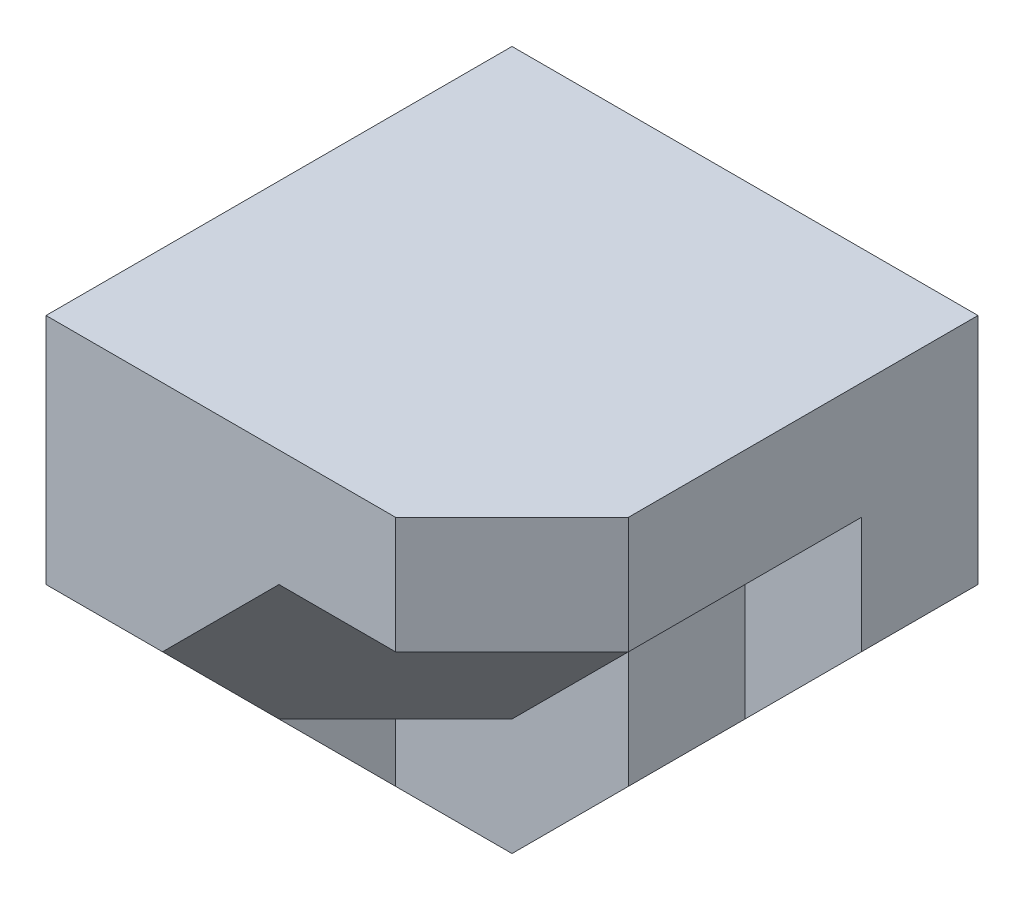
SolidWorks part; units mm, degrees
ref_plane "Front Plane" through (0, 0, 0) normal (0, 0, 1) x (1, 0, 0)
ref_plane "Top Plane" through (0, 0, 0) normal (0, 1, 0) x (1, 0, 0)
ref_plane "Right Plane" through (0, 0, 0) normal (1, 0, 0) x (0, 0, -1)
sketch "Sketch1" plane through (0, 0, 0) normal (0, 0, 1) x (1, 0, 0)
  line L1 (0, 0) -> (40, 0)
  line L2 (0, 0) -> (0, 40)
  line L3 (0, 40) -> (40, 40)
  line L4 (40, 0) -> (40, 40)
  dimension "D1" = 40
  dimension "D2" = 40
extrude "Boss-Extrude1" add sketch "Sketch1" along normal blind 20
sketch "Sketch2" plane through (0, 0, 20) normal (0, 0, 1) x (1, 0, 0)
  line L0 (20, 0) -> (40, 20)
  line L1 (0, 0) -> (40, 0) construction
  line L2 (40, 0) -> (40, 40) construction
  line L3 (40, 20) -> (40, 0)
  line L4 (40, 0) -> (20, 0)
  dimension "D1" = 20
  dimension "D2" = 20
extrude "Cut-Extrude1" cut sketch "Sketch2" against normal blind 20
sketch "Sketch3" plane through (0, 0, 20) normal (0, 0, 1) x (1, 0, 0)
  line L0 (30, 10) -> (30, 20)
  line L1 (40, 20) -> (20, 0) construction
  line L2 (30, 20) -> (40, 30)
  line L3 (40, 20) -> (40, 40) construction
  line L4 (40, 30) -> (40, 20)
  line L5 (30, 10) -> (40, 20)
  line L6 (40, 20) -> (40, 30)
  line M5 (20, 0) -> (40, 20)
  line M6 (40, 20) -> (40, 40)
  dimension "D1" = 10
  dimension "D2" = 10
  dimension "D3" = 10
extrude "Cut-Extrude2" cut sketch "Sketch3" against normal blind 10 contours L2 L0 M5 M6
sketch "Sketch4" plane through (40, 0, 0) normal (1, 0, 0) x (0, 0, -1)
  line L1 (-20, 40) -> (-40, 40)
  line L2 (-20, 40) -> (-20, 30)
  line L3 (-20, 30) -> (-40, 30)
  line L4 (-40, 40) -> (-40, 30)
  dimension "D1" = 10
  dimension "D2" = 20
extrude "Boss-Extrude2" add sketch "Sketch4" against normal blind 40
sketch "Sketch5" plane through (0, 30, 0) normal (0, -1, 0) x (-1, 0, 0)
  line L0 (-30, -40) -> (-40, -40)
  line L1 (0, -40) -> (-40, -40) construction
  line L2 (-40, -40) -> (-40, -30)
  line L3 (-40, -40) -> (-40, -20) construction
  line L4 (-40, -30) -> (-30, -40)
  dimension "D1" = 10
  dimension "D2" = 10
extrude "Cut-Extrude3" cut sketch "Sketch5" against normal blind 40
sketch "Sketch6" plane through (0, 0, 0) normal (-1, 0, 0) x (0, 0, 1)
  line L1 (20, 30) -> (40, 30)
  line L2 (20, 30) -> (20, 20)
  line L3 (20, 20) -> (40, 20)
  line L4 (40, 30) -> (40, 20)
  dimension "D1" = 10
  dimension "D2" = 20
extrude "Boss-Extrude3" add sketch "Sketch6" against normal blind 10
sketch "Sketch7" plane through (0, 0, 0) normal (-1, 0, 0) x (0, 0, 1)
  line L0 (30, 20) -> (30, 10)
  line L1 (20, 20) -> (40, 20) construction
  line L2 (30, 10) -> (20, 0)
  line L3 (20, 0) -> (20, 20)
  line L4 (20, 20) -> (30, 20)
  dimension "D1" = 10
extrude "Boss-Extrude4" add sketch "Sketch7" against normal blind 10
sketch "Sketch8" plane through (0, 0, 40) normal (0, 0, 1) x (1, 0, 0)
  line L0 (10, 20) -> (20, 30)
  line L1 (10, 30) -> (30, 30) construction
  line L2 (20, 30) -> (10, 30)
  line L3 (10, 30) -> (10, 20)
extrude "Boss-Extrude5" add sketch "Sketch8" against normal blind 27
sketch "Sketch9" plane through (0, 0, 20) normal (0, 0, 1) x (1, 0, 0)
  line L0 (10, 20) -> (20, 30)
  line L1 (20, 30) -> (40, 30)
  line L2 (40, 30) -> (30, 20)
  line L3 (30, 20) -> (20, 10)
  line L4 (20, 10) -> (10, 10)
  line L5 (10, 20) -> (10, 0) construction
  line L6 (10, 10) -> (10, 20)
  dimension "D1" = 180
extrude "Boss-Extrude6" add sketch "Sketch9" along normal blind 20
sketch3d "3DSketch1"
  line L0 (40, 30, 10) -> (40, 30, 30) construction
  line L1 (0, 40, 40) -> (0, 20, 40) construction
  line L2 (0, 40, 40) -> (30, 40, 40) construction
  line L3 (20, 30, 40) -> (40, 30, 20)
  line L4 (10, 10, 20) -> (20, 10, 20) construction
  line L5 (10, 10, 30) -> (20, 10, 20)
  line L6 (10, 10, 30) -> (10, 20, 40)
  line L7 (10, 20, 40) -> (20, 30, 40)
  line L8 (20, 10, 20) -> (40, 30, 20)
  point P0 (10, 10, 20)
  point P1 (10, 10, 30)
  point P3 (10, 20, 40)
  point P5 (20, 30, 40)
  point P7 (40, 30, 20)
  point P20 (20, 10, 20)
  dimension "D1" = 10
  dimension "D2" = 20
  dimension "D3" = 10
  dimension "D4" = 10
extrude "Cut-Extrude4" cut sketch "3DSketch1" along direction (-1, 0, 0) on the side against the normal blind 20 contours L6 L7 L3 L8 L5
